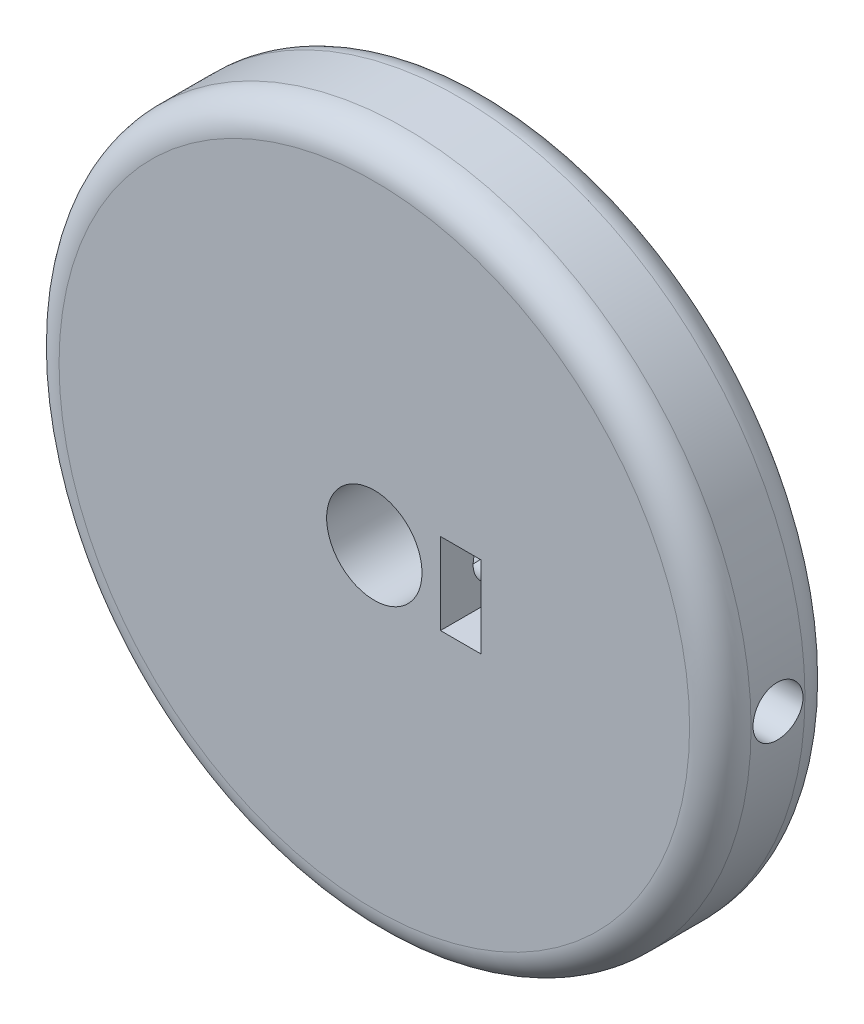
SolidWorks part; units mm, degrees
ref_plane "Front Plane" through (0, 0, 0) normal (0, 0, 1) x (1, 0, 0)
ref_plane "Top Plane" through (0, 0, 0) normal (0, 1, 0) x (1, 0, 0)
ref_plane "Right Plane" through (0, 0, 0) normal (1, 0, 0) x (0, 0, -1)
sketch "Sketch1" plane through (0, 0, 0) normal (0, 0, 1) x (1, 0, 0)
  circle A0 centre (0, 0) radius 45
  circle A1 centre (0, 0) radius 6.2
  dimension "D1" = 12.4
  dimension "D2" = 90
extrude "Boss-Extrude1" add sketch "Sketch1" along normal mid plane 15
sketch "Sketch2" plane through (0, 0, 7.5) normal (0, 0, 1) x (1, 0, 0)
  line L0 (8.6, 0) -> (0, 0)
  line L1 (8.6, 5.3) -> (13.9, 5.3)
  line L2 (8.6, 5.3) -> (8.6, -5.3)
  line L3 (8.6, -5.3) -> (13.9, -5.3)
  line L4 (13.9, 5.3) -> (13.9, -5.3)
  circle A0 centre (0, 0) radius 6.2 construction
  dimension "D3" = 8.6
  dimension "D1" = 10.6
  dimension "D2" = 5.3
extrude "Cut-Extrude1" cut sketch "Sketch2" against normal blind 13 contours L4 L1 L2 L3
sketch "Sketch3" plane through (8.6, 0, 0) normal (1, 0, 0) x (0, 0, -1)
  circle A0 centre (0, 0) radius 3.25
  dimension "D1" = 6.5
extrude "Cut-Extrude2" cut sketch "Sketch3" against normal blind 13 and the other way through all
fillet "Fillet1" radius 4 2 edges at (45, 0, -7.5) (45, 0, 7.5)
